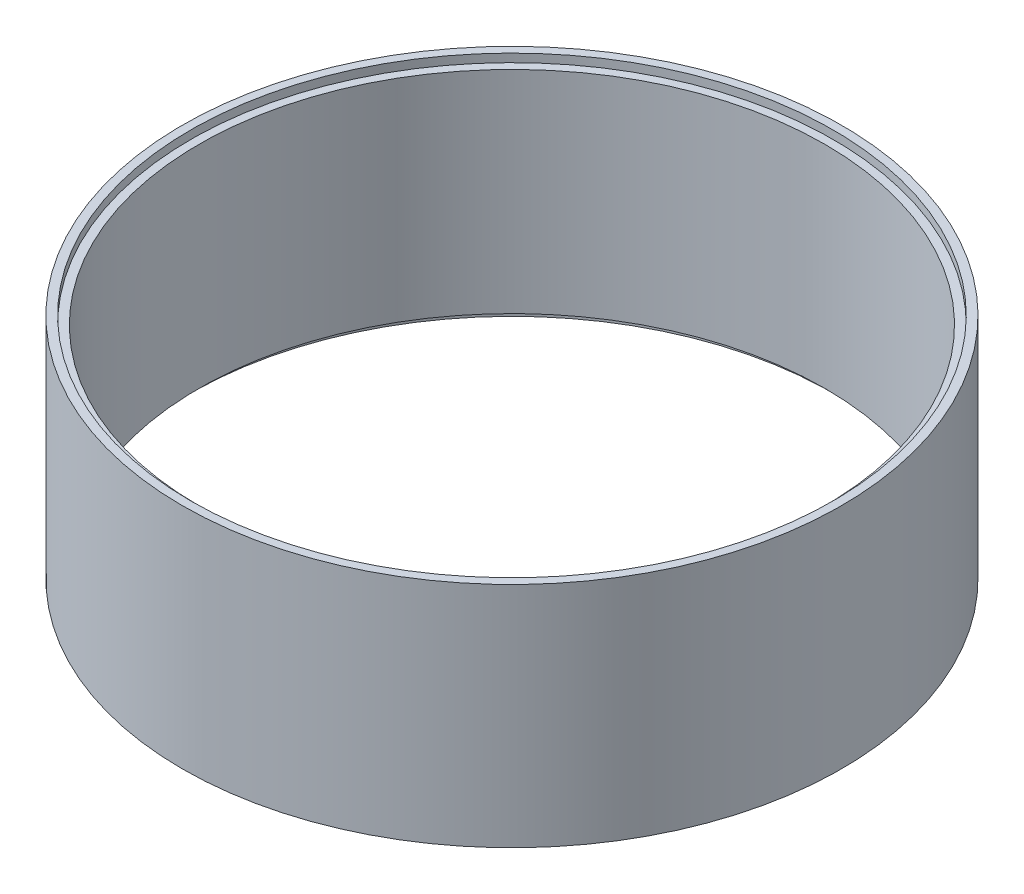
SolidWorks part; units mm, degrees
ref_plane "Plan de face" through (0, 0, 0) normal (0, 0, 1) x (1, 0, 0)
ref_plane "Plan de dessus" through (0, 0, 0) normal (0, 1, 0) x (1, 0, 0)
ref_plane "Plan de droite" through (0, 0, 0) normal (1, 0, 0) x (0, 0, -1)
sketch "Esquisse2" plane through (0, 0, 0) normal (0, 1, 0) x (1, 0, 0)
  circle A0 centre (0, 0) radius 155 construction
  circle A1 centre (0, 0) radius 151
  circle A2 centre (0, 0) radius 159
  dimension "D1" = 310
  dimension "D2" = 8
  dimension "D3" = 4
extrude "Boss.-Extru.1" add sketch "Esquisse2" along normal mid plane 110
sketch "Esquisse3" plane through (0, 55, 0) normal (0, 1, 0) x (1, 0, 0)
  circle A0 centre (0, 0) radius 155
  circle A1 centre (0, 0) radius 151 construction
  dimension "D1" = 4
extrude "Enlèv. mat.-Extru.1" cut sketch "Esquisse3" against normal blind 4
mirror "Symétrie1" about plane through (0, 0, 0) normal (0, 1, 0) of "Enlèv. mat.-Extru.1"
equation "\"D3@Esquisse2\"=\"D2@Esquisse2\"/2"
